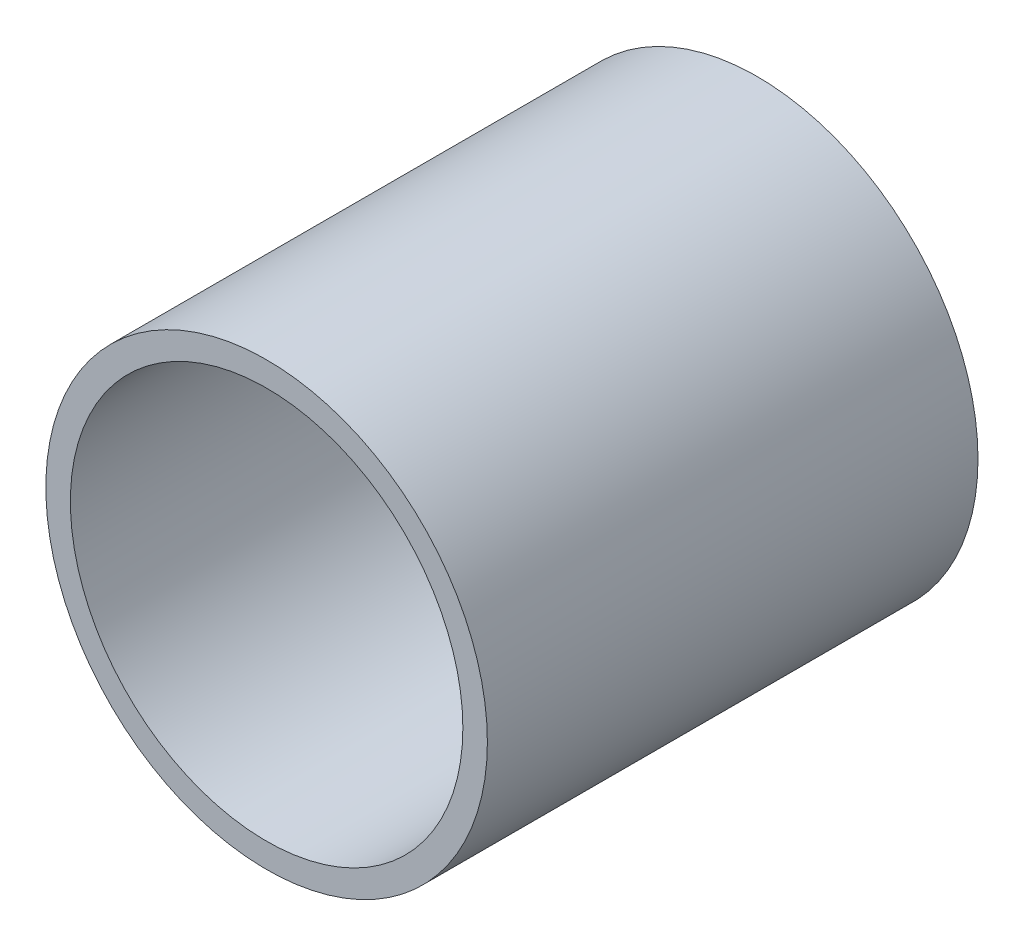
SolidWorks part; units mm, degrees
material "Aluminum Bronze"
ref_plane "Front Plane" through (0, 0, 0) normal (0, 0, 1) x (1, 0, 0)
ref_plane "Top Plane" through (0, 0, 0) normal (0, 1, 0) x (1, 0, 0)
ref_plane "Right Plane" through (0, 0, 0) normal (1, 0, 0) x (0, 0, -1)
sketch "Sketch1" plane through (0, 0, 0) normal (0, 0, 1) x (1, 0, 0)
  circle A0 centre (0, 0) radius 28.575
  circle A1 centre (0, 0) radius 25.4
  dimension "D1" = 57.15
  dimension "ID" = 50.8
extrude "Extrude1" add sketch "Sketch1" along normal mid plane 63.5
sketch "Sketch2" plane through (0, 0, 0) normal (1, 0, 0) x (0, 0, -1)
  line L0 (-31.75, -25.4) -> (31.75, -25.4) construction
  line L3 (31.75, 25.4) -> (-31.75, 25.4) construction
  line L5 (-31.75, -25.4) -> (31.75, -25.4)
  line L6 (31.75, 25.4) -> (-31.75, 25.4)
sketch "Sketch4" plane through (0, 0, 31.75) normal (0, 0, 1) x (1, 0, 0)
  line L0 (0, 0) -> (-17.9605, 17.9605)
  line L1 (0, -34.925) -> (0, 34.925) construction
  circle A0 centre (0, 0) radius 25.4 construction
  dimension "D1" = 45
